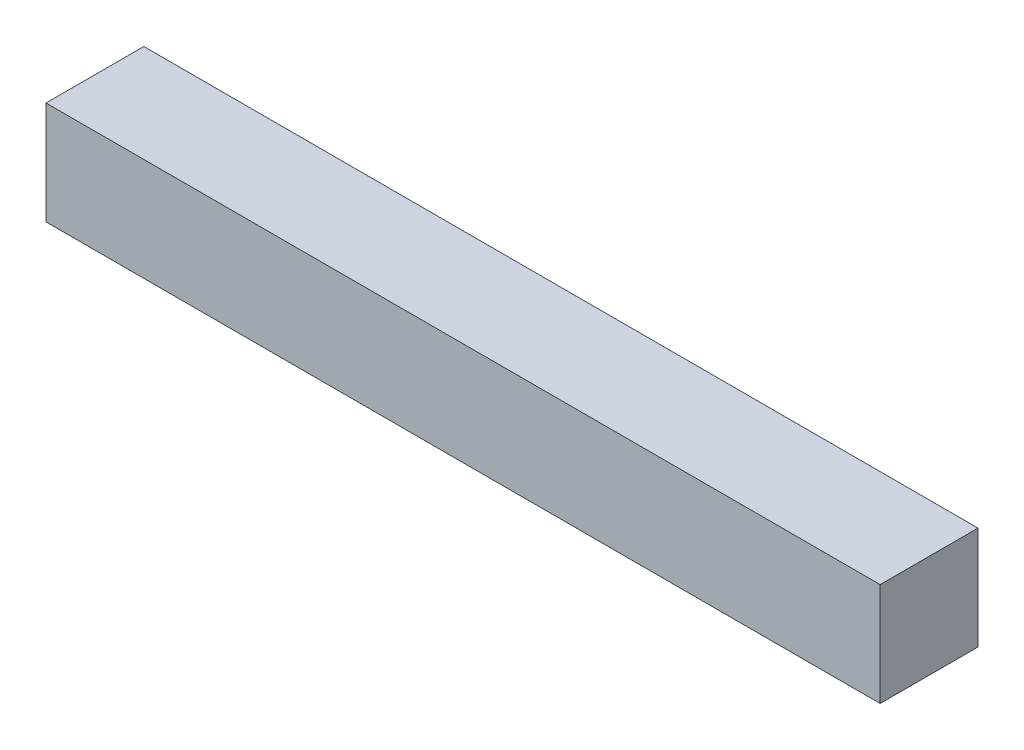
SolidWorks part; units mm, degrees
ref_plane "Front Plane" through (0, 0, 0) normal (0, 0, 1) x (1, 0, 0)
ref_plane "Top Plane" through (0, 0, 0) normal (0, 1, 0) x (1, 0, 0)
ref_plane "Right Plane" through (0, 0, 0) normal (1, 0, 0) x (0, 0, -1)
sketch "Sketch1" plane through (0, 0, 0) normal (0, 0, 1) x (1, 0, 0)
  line L1 (0, 0) -> (40.5, 0)
  line L2 (0, 0) -> (0, 5)
  line L3 (0, 5) -> (40.5, 5)
  line L4 (40.5, 0) -> (40.5, 5)
  dimension "D1" = 5
  dimension "D2" = 40.5
extrude "Boss-Extrude1" add sketch "Sketch1" along normal blind 4.75
